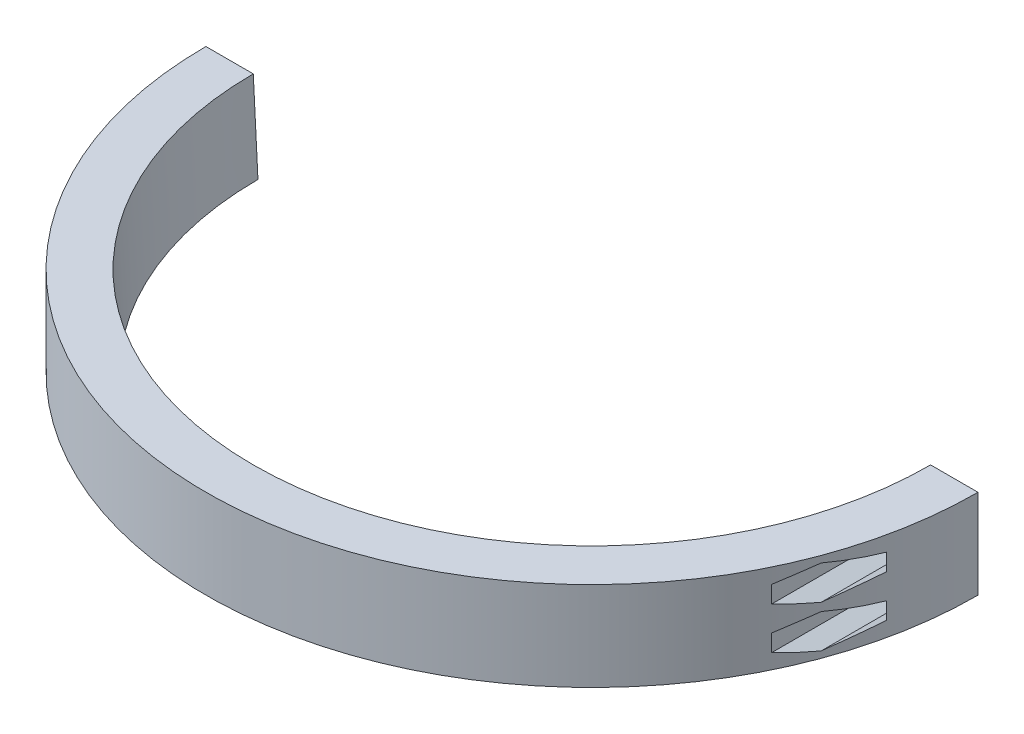
SolidWorks part; units mm, degrees
material "ABS"
ref_plane "Front Plane" through (0, 0, 0) normal (0, 0, 1) x (1, 0, 0)
ref_plane "Top Plane" through (0, 0, 0) normal (0, 1, 0) x (1, 0, 0)
ref_plane "Right Plane" through (0, 0, 0) normal (1, 0, 0) x (0, 0, -1)
sketch "REFERENCE" plane through (0, 0, 0) normal (0, 0, 1) x (1, 0, 0)
  line L0 (0, 0) -> (45, 0) construction
  line L1 (0, 50.3555) -> (0, -50.3555) construction
  line L2 (45, 50.3555) -> (45, -50.3555) construction
  line L3 (45, 0) -> (42.5, -47.7028) construction
  line L4 (40, -105) -> (42.1213, -107.1213) construction
  line L5 (42.5, -47.7028) -> (45.5, -47.7028) construction
  line L6 (45, 0) -> (48, 0) construction
  line L7 (48, 0) -> (45.5, -47.7028) construction
  line L8 (0, -50.3555) -> (0, -113.6539) construction
  arc A0 (42.5, -47.7028) -> (40, -105) centre (0, -74.5516) cw construction
  arc A1 (45.5, -47.7028) -> (42.1213, -107.1213) centre (0, -74.9209) cw construction
  point P5 (0, 0)
  point P8 (45, 0)
  point P9 (45, 0)
  dimension "D7" = 50.2703
  dimension "D1" = 45
  dimension "D2" = 3
  dimension "D3" = 105
  dimension "D4" = 3
  dimension "D5" = 40
  dimension "D6" = 42.5
sketch "Sketch3" plane through (0, 0, 0) normal (0, 0, 1) x (1, 0, 0)
  line L5 (48.25, 0) -> (47.5844, -12.7)
  line L6 (47.5844, -12.7) -> (55, -12.7)
  line L7 (55, -12.7) -> (55, 0)
  line L8 (55, 0) -> (48.25, 0)
  line L9 (48, 0) -> (45.5, -47.7028) construction
  dimension "D1" = 48.25
  dimension "D2" = 55
  dimension "D3" = 12.7
revolve "Revolve2" add sketch "Sketch3" angle 180 about L1
ref_plane "Plane1" through (0, 0, 55) normal (0, 0, 1) x (1, 0, 0)
hole_wizard "CBORE for M2 SHCS1" [suppressed] positions "Sketch6" profile "Sketch8" counterbore size "M2" standard "ANSI Metric"
sketch "Sketch6" plane through (0, 0, 55) normal (0, 0, 1) x (1, 0, 0)
  line L0 (51.625, -3.35) -> (51.625, -9.35)
  line L2 (55, 0) -> (48.25, 0) construction
  line L3 (55, -12.7) -> (55, 0) construction
  point P0 (51.625, -3.35)
  point P2 (51.625, -9.35)
  point P12 (51.625, 0)
  point P13 (51.625, -6.35)
  point P16 (55, -6.35)
  dimension "D1" = 0
  dimension "D2" = 0
  dimension "D3" = 6
sketch "Sketch8" plane through (51.625, -3.35, 55) normal (1, 0, 0) x (0, -1, 0)
  line L0 (0, 0) -> (0, 55)
  line L1 (0, 55) -> (1.1, 55)
  line L3 (1.1, 55) -> (1.1, 50)
  line L4 (1.1, 50) -> (2.2, 50)
  line L5 (2.2, 50) -> (2.2, 0)
  line L7 (2.2, 0) -> (0, 0)
  line L11 (0, -6.35) -> (0, 107.95) construction
  dimension "Thru Hole Dia." = 2.2
  dimension "Thru Hole Depth" = 55
  dimension "C'Bore Dia." = 4.4
  dimension "C'Bore Depth" = 50
mirror "Mirror1" [suppressed] about plane through (0, 0, 0) normal (1, 0, 0)
sketch "Sketch9" plane through (0, 0, 55) normal (0, 0, 1) x (1, 0, 0)
  line L0 (51.625, -3.35) -> (51.625, -9.35) construction
  line L1 (55, 0) -> (48.25, 0) construction
  line L2 (55, -12.7) -> (55, 0) construction
  line L4 (53.725, -4.5624) -> (53.725, -2.1376)
  line L5 (53.725, -2.1376) -> (51.625, -0.9251)
  line L6 (51.625, -0.9251) -> (49.525, -2.1376)
  line L7 (49.525, -2.1376) -> (49.525, -4.5624)
  line L8 (49.525, -4.5624) -> (51.625, -5.7749)
  line L9 (51.625, -5.7749) -> (53.725, -4.5624)
  line L10 (53.725, -10.5624) -> (53.725, -8.1376)
  line L11 (53.725, -8.1376) -> (51.625, -6.9251)
  line L12 (51.625, -6.9251) -> (49.525, -8.1376)
  line L13 (49.525, -8.1376) -> (49.525, -10.5624)
  line L14 (49.525, -10.5624) -> (51.625, -11.7749)
  line L15 (51.625, -11.7749) -> (53.725, -10.5624)
  circle A0 centre (51.625, -3.35) radius 2.1 construction
  circle A1 centre (51.625, -9.35) radius 2.1 construction
  point P0 (51.625, -3.35)
  point P1 (51.625, -9.35)
  point P6 (51.625, 0)
  point P7 (51.625, -6.35)
  point P10 (55, -6.35)
  dimension "D1" = 0
  dimension "D2" = 0
  dimension "D3" = 6
  dimension "D4" = 4.2
  dimension "D5" = 4.2
extrude "Cut-Extrude1" cut sketch "Sketch9" against normal blind 50
hole_wizard "Ø2.0mm Dowel Hole1" positions "Sketch10" profile "Sketch11" hole size "Ø2.0" standard "ANSI Metric" end condition through all
sketch "Sketch10" plane through (0, 0, 5) normal (0, 0, 1) x (1, 0, 0)
  line L0 (53.725, -2.1376) -> (49.525, -4.5624)
  line L2 (49.525, -2.1376) -> (53.725, -4.5624)
  line L4 (53.725, -8.1376) -> (49.525, -10.5624)
  line L6 (49.525, -8.1376) -> (53.725, -10.5624)
  line L7 (53.725, -8.1376) -> (53.725, -10.5624) construction
  line L8 (53.725, -10.5624) -> (53.725, -8.1376) construction
  point P29 (51.625, -3.35)
  point P31 (51.625, -9.35)
sketch "Sketch11" plane through (51.625, -9.35, 5) normal (1, 0, 0) x (0, -1, 0)
  line L0 (0, 0) -> (0, 5)
  line L1 (0, 5) -> (1.15, 5)
  line L2 (1.15, 5) -> (1.15, 0)
  line L5 (1.15, 0) -> (0, 0)
  line L11 (0, -6.35) -> (0, 107.95) construction
  dimension "Thru Hole Dia." = 2.3
  dimension "Thru Hole Depth" = 5
mirror "Mirror2" about plane through (0, 0, 0) normal (1, 0, 0) of "Cut-Extrude1", "Ø2.0mm Dowel Hole1"
ref_plane "Plane2" through (0, 0, 0) normal (-0.7071, 0, 0.7071) x (0.7071, 0, 0.7071)
sketch "Sketch13" plane through (0, 0, 0) normal (-0.7071, 0, 0.7071) x (0.7071, 0, 0.7071)
  line L0 (55, 0) -> (-38.8909, 0) construction
  circle A0 centre (0, -6.35) radius 1.65
  dimension "D3" = 3.3
  dimension "D1" = 6.35
  dimension "D2" = 0
extrude "Cut-Extrude2" cut sketch "Sketch13" against normal mid plane 200
